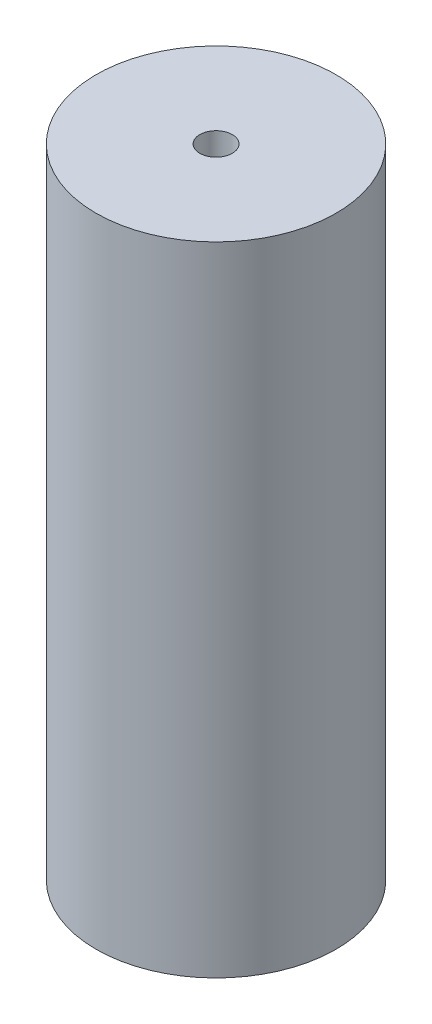
SolidWorks part; units mm, degrees
ref_plane "Front Plane" through (0, 0, 0) normal (0, 0, 1) x (1, 0, 0)
ref_plane "Top Plane" through (0, 0, 0) normal (0, 1, 0) x (1, 0, 0)
ref_plane "Right Plane" through (0, 0, 0) normal (1, 0, 0) x (0, 0, -1)
sketch "Sketch1" plane through (0, 0, 0) normal (0, 1, 0) x (1, 0, 0)
  circle A0 centre (0, 0) radius 23.9141
  dimension "D1" = 47.8282
extrude "Boss-Extrude1" add sketch "Sketch1" along normal blind 127
sketch "Sketch2" plane through (0, 127, 0) normal (0, 1, 0) x (1, 0, 0)
  circle A0 centre (0, 0) radius 3.2385
  dimension "D1" = 6.477
extrude "Cut-Extrude1" cut sketch "Sketch2" against normal up to next
